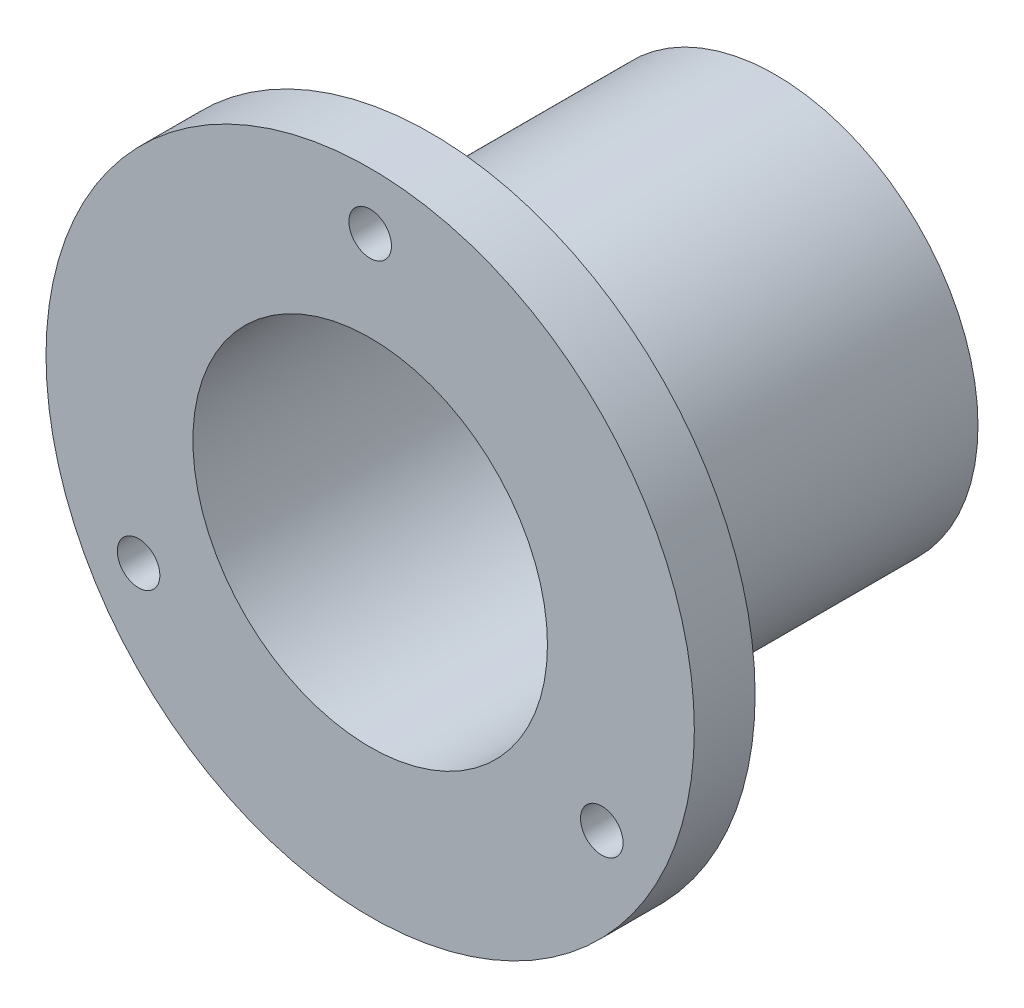
SolidWorks part; units mm, degrees
material "6061 Alloy"
ref_plane "Front Plane" through (0, 0, 0) normal (0, 0, 1) x (1, 0, 0)
ref_plane "Top Plane" through (0, 0, 0) normal (0, 1, 0) x (1, 0, 0)
ref_plane "Right Plane" through (0, 0, 0) normal (1, 0, 0) x (0, 0, -1)
sketch "Sketch1" plane through (0, 0, 0) normal (0, 0, 1) x (1, 0, 0)
  circle A0 centre (0, 0) radius 20
  circle A1 centre (0, 0) radius 17.5
  dimension "D1" = 40
  dimension "D2" = 2.5
extrude "Boss-Extrude1" add sketch "Sketch1" along normal mid plane 40
sketch "Sketch2" plane through (0, 0, 20) normal (0, 0, 1) x (1, 0, 0)
  circle A2 centre (0, 0) radius 32
  circle A3 centre (0, 0) radius 32
  circle A5 centre (0, 0) radius 20 construction
  circle A6 centre (0, 0) radius 20
  dimension "D1" = 12
extrude "Boss-Extrude2" add sketch "Sketch2" against normal blind 6 separate body
hole_wizard "M5 Tapped Hole1" positions "Sketch3" profile "Sketch4" tap size "M5" standard "ISO" end condition through all
sketch "Sketch3" plane through (0, 0, 14) normal (0, 0, -1) x (-1, 0, 0)
  line L0 (0, 0) -> (0, 26.4) construction
  line L1 (0, 32) -> (0, 20) construction
  circle A4 centre (0, 0) radius 26.4
  circle A8 centre (0, 0) radius 20 construction
  circle A9 centre (0, 0) radius 32 construction
  point P0 (0, 26.4)
  dimension "D1" = 26.4
sketch "Sketch4" plane through (0, 26.4, 14) normal (1, 0, 0) x (0, 1, 0)
  line L0 (0, 0) -> (0, 6)
  line L1 (0, 6) -> (2.1, 6)
  line L2 (2.1, 6) -> (2.1, 0)
  line L5 (2.1, 0) -> (0, 0)
  line L11 (0, -6.35) -> (0, 107.95) construction
  dimension "Thru Tap Drill Dia." = 4.2
  dimension "Thru Tap Drill Depth" = 6
cosmetic thread "Hole Thread1" parameters "D2"=5
pattern_circular "CirPattern1" count 3 over 360 about axis through (0, 0, 0) along (0, 0, 1) of "M5 Tapped Hole1"
cosmetic thread "Hole Thread2" parameters "D2"=5
cosmetic thread "Hole Thread3" parameters "D2"=5
chamfer "Chamfer1" distance 1 angle 45 1 edges at (17.5, 0, -20)
combine bodies "Combine1" operation type add bodies to combine 101 104
fillet "Fillet3" radius 1 1 edges at (20, 0, 14)
